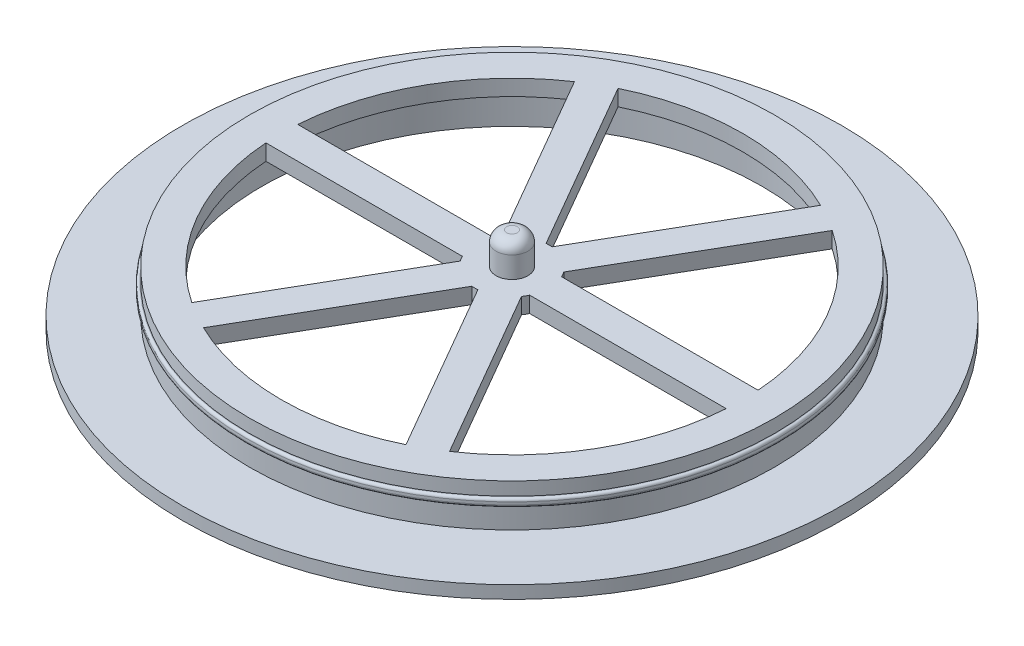
SolidWorks part; units mm, degrees
material "ABS"
ref_plane "Front Plane" through (0, 0, 0) normal (0, 0, 1) x (1, 0, 0)
ref_plane "Top Plane" through (0, 0, 0) normal (0, 1, 0) x (1, 0, 0)
ref_plane "Right Plane" through (0, 0, 0) normal (1, 0, 0) x (0, 0, -1)
sketch "Sketch1" plane through (0, 0, 0) normal (0, 1, 0) x (1, 0, 0)
  circle A0 centre (0, 0) radius 31
  circle A1 centre (0, 0) radius 23.5
  dimension "D1" = 62
  dimension "D2" = 47
extrude "Boss-Extrude1" add sketch "Sketch1" along normal blind 1.2
sketch "Sketch2" plane through (0, 1.2, 0) normal (0, 1, 0) x (1, 0, 0)
  circle A0 centre (0, 0) radius 23.5 construction
  circle A1 centre (0, 0) radius 23.5
  circle A2 centre (0, 0) radius 24.7
  dimension "D1" = 1.2
extrude "Boss-Extrude2" add sketch "Sketch2" along normal blind 4
sketch "Sketch3" plane through (0, 5.2, 0) normal (0, 1, 0) x (1, 0, 0)
  circle A0 centre (0, 0) radius 25
  circle A1 centre (0, 0) radius 24.7 construction
  circle A2 centre (0, 0) radius 24.7
  dimension "D1" = 0.3
extrude "Boss-Extrude3" add sketch "Sketch3" along normal blind 0.75 from offset 2 offset against normal yes
fillet "Fillet1" radius 0.25 2 edges at (0, 3.2, 25) (0, 3.95, 25)
sketch "Sketch4" plane through (0, 5.2, 0) normal (0, 1, 0) x (1, 0, 0)
  line L0 (-24.7, 0) -> (24.7, 0) construction
  line L1 (-12.35, 21.3908) -> (12.35, -21.3908) construction
  line L2 (12.35, 21.3908) -> (-12.35, -21.3908) construction
  line L3 (13.6262, -20.6013) -> (2.8802, -1.9886)
  line L4 (11.0282, -22.1013) -> (0.2821, -3.4886)
  line L5 (24.6544, 1.5) -> (3.1623, 1.5)
  line L6 (24.6544, -1.5) -> (3.1623, -1.5)
  line L7 (-11.0288, -22.101) -> (-0.2829, -3.4886)
  line L8 (11.0275, 22.1017) -> (0.2813, 3.4887)
  line L9 (0.866, -1.5) -> (0.8652, -1.5)
  line L10 (1.7321, 0) -> (1.7317, 0.0007)
  line L11 (1.7313, 0) -> (1.7317, 0.0007)
  line L12 (2.8797, 1.9892) -> (13.6257, 20.6017)
  line L13 (-0.2821, 3.4886) -> (-11.0282, 22.1013)
  line L14 (-0.866, 1.5) -> (-0.8668, 1.5)
  line L15 (-0.8664, 1.5007) -> (-0.8668, 1.5)
  line L16 (-1.7325, 0.0007) -> (-1.7328, 0)
  line L17 (-3.1623, 1.5) -> (-24.6544, 1.5)
  line L18 (-2.8802, 1.9886) -> (-13.6262, 20.6013)
  line L19 (-1.7321, 0) -> (-1.7325, 0.0007)
  line L20 (-2.8806, -1.988) -> (-13.6268, -20.601)
  line L21 (-3.1623, -1.5) -> (-24.6544, -1.5)
  line L22 (0.8652, -1.5) -> (0.8656, -1.4993)
  circle A0 centre (0, 0) radius 24.7 construction
  circle A1 centre (0, 0) radius 24.7 construction
  arc A2 (11.0282, -22.1013) -> (13.6262, -20.6013) centre (0, 0) ccw
  circle A3 centre (0, 0) radius 24.7 construction
  arc A4 (24.6544, -1.5) -> (24.6544, 1.5) centre (0, 0) ccw
  arc A5 (13.6257, 20.6017) -> (11.0275, 22.1017) centre (0, 0) ccw
  arc A6 (-11.0282, 22.1013) -> (-13.6262, 20.6013) centre (0, 0) ccw
  arc A7 (-24.6544, 1.5) -> (-24.6544, -1.5) centre (0, 0) ccw
  arc A8 (-13.6268, -20.601) -> (-11.0288, -22.101) centre (0, 0) ccw
  arc A9 (-0.2829, -3.4886) -> (0.2821, -3.4886) centre (0, 0) ccw
  arc A10 (2.8802, -1.9886) -> (3.1623, -1.5) centre (0, 0) ccw
  arc A11 (3.1623, 1.5) -> (2.8797, 1.9892) centre (0, 0) ccw
  arc A12 (0.2813, 3.4887) -> (-0.2821, 3.4886) centre (0, 0) ccw
  arc A13 (-2.8802, 1.9886) -> (-3.1623, 1.5) centre (0, 0) ccw
  arc A14 (-3.1623, -1.5) -> (-2.8806, -1.988) centre (0, 0) ccw
  point P4 (0, 0)
  point P10 (0, 0)
  point P13 (0, 0)
  dimension "D9" = 7
  dimension "D1" = 60
  dimension "D2" = 60
  dimension "D3" = 1.5
  dimension "D4" = 3
  dimension "D5" = 1.5
  dimension "D6" = 3
  dimension "D7" = 1.5
  dimension "D8" = 3
extrude "Boss-Extrude4" add sketch "Sketch4" against normal blind 1.5
sketch "Sketch5" plane through (0, 5.2, 0) normal (0, 1, 0) x (1, 0, 0)
  circle A0 centre (0, 0) radius 21.7
  circle A1 centre (0, 0) radius 24.7 construction
  circle A2 centre (0, 0) radius 24.7
  dimension "D1" = 3
extrude "Boss-Extrude5" add sketch "Sketch5" against normal blind 1.5
sketch "Sketch6" plane through (0, 5.2, 0) normal (0, 1, 0) x (1, 0, 0)
  circle A0 centre (0, 0) radius 1.5
  dimension "D1" = 3
extrude "Boss-Extrude6" add sketch "Sketch6" along normal blind 3
fillet "Fillet2" radius 1 1 edges at (0, 8.2, 1.5)
equation "\"2.5.00mm\"=0"
